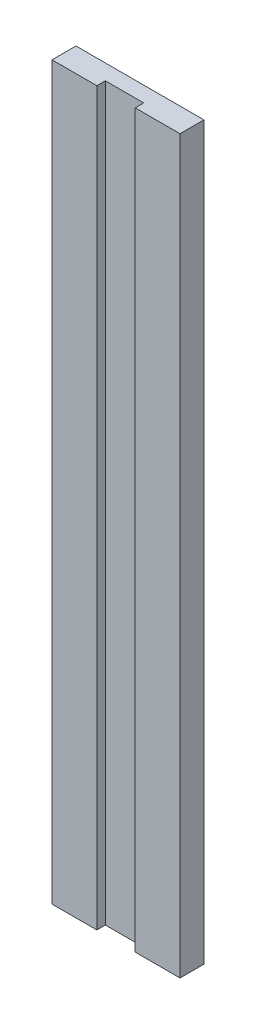
SolidWorks part; units mm, degrees
ref_plane "Front Plane" through (0, 0, 0) normal (0, 0, 1) x (1, 0, 0)
ref_plane "Top Plane" through (0, 0, 0) normal (0, 1, 0) x (1, 0, 0)
ref_plane "Right Plane" through (0, 0, 0) normal (1, 0, 0) x (0, 0, -1)
sketch "Sketch1" plane through (0, 0, 0) normal (0, 0, 1) x (1, 0, 0)
  line L1 (35, 200) -> (-35, 200)
  line L2 (35, 200) -> (35, -200)
  line L3 (35, -200) -> (-35, -200)
  line L4 (-35, 200) -> (-35, -200)
  line L5 (35, 200) -> (-35, -200) construction
  line L6 (35, -200) -> (-35, 200) construction
  point P0 (0, 0)
  dimension "D1" = 400
  dimension "D2" = 70
extrude "Boss-Extrude1" add sketch "Sketch1" along normal blind 8.45
sketch "Sketch3" plane through (0, 0, 8.45) normal (0, 0, 1) x (1, 0, 0)
  line L0 (-35, -200) -> (35, -200) construction
  line L1 (35, 200) -> (10.5, 200)
  line L2 (35, 200) -> (35, -200)
  line L3 (35, -200) -> (10.5, -200)
  line L4 (10.5, 200) -> (10.5, -200)
  line L5 (35, 200) -> (-35, 200) construction
  line L6 (-35, -200) -> (-10.5, -200)
  line L7 (-35, -200) -> (-35, 200)
  line L8 (-35, 200) -> (-10.5, 200)
  line L9 (-10.5, -200) -> (-10.5, 200)
  dimension "D1" = 21
extrude "Boss-Extrude2" add sketch "Sketch3" along normal blind 13.1 from surface at -8.45 starting at face at (0, 0, 0)
fillet "Fillet1" [suppressed] radius 5
sketch "Sketch4" plane through (0, 0, 13.1) normal (0, 0, 1) x (1, 0, 0)
  line L0 (-22.75, 200) -> (-22.75, 185) construction
  line L3 (-35, 200) -> (-10.5, 200) construction
  line L4 (-22.75, 185) -> (-22.75, 123.3333) construction
  line L5 (-22.75, 123.3333) -> (-22.75, 61.6667) construction
  line L6 (-22.75, 61.6667) -> (-22.75, 0) construction
  line L7 (-22.75, 0) -> (-22.75, -61.6667) construction
  line L8 (-22.75, -61.6667) -> (-22.75, -123.3333) construction
  line L9 (-22.75, -123.3333) -> (-22.75, -185) construction
  line L10 (-22.75, -185) -> (-22.75, -200) construction
  line L11 (-10.5, -200) -> (-35, -200) construction
  line L12 (0, 200) -> (0, -200) construction
  line L13 (10.5, 200) -> (-10.5, 200) construction
  line L14 (-10.5, -200) -> (10.5, -200) construction
  circle A0 centre (-22.75, 185) radius 2.75
  circle A1 centre (-22.75, 123.3333) radius 2.75
  circle A2 centre (-22.75, 61.6667) radius 2.75
  circle A3 centre (-22.75, 0) radius 2.75
  circle A4 centre (-22.75, -61.6667) radius 2.75
  circle A5 centre (-22.75, -123.3333) radius 2.75
  circle A6 centre (-22.75, -185) radius 2.75
  circle A7 centre (22.75, -185) radius 2.75
  circle A8 centre (22.75, -123.3333) radius 2.75
  circle A9 centre (22.75, -61.6667) radius 2.75
  circle A10 centre (22.75, 0) radius 2.75
  circle A11 centre (22.75, 61.6667) radius 2.75
  circle A12 centre (22.75, 123.3333) radius 2.75
  circle A13 centre (22.75, 185) radius 2.75
  dimension "D2" = 5.5
  dimension "D1" = 15
extrude "Cut-Extrude1" [suppressed] cut sketch "Sketch4" against normal through all
sketch "Sketch5" [suppressed] plane through (0, 0, 13.1) normal (0, 0, 1) x (1, 0, 0)
  circle A0 centre (-22.75, 185) radius 4.5
  circle A1 centre (22.75, 185) radius 4.5
  circle A2 centre (22.75, 123.3333) radius 4.5
  circle A3 centre (-22.75, 123.3333) radius 4.5
  circle A4 centre (-22.75, 61.6667) radius 4.5
  circle A5 centre (22.75, 61.6667) radius 4.5
  circle A6 centre (22.75, 0) radius 4.5
  circle A7 centre (-22.75, 0) radius 4.5
  circle A8 centre (-22.75, -61.6667) radius 4.5
  circle A9 centre (22.75, -61.6667) radius 4.5
  circle A10 centre (22.75, -123.3333) radius 4.5
  circle A11 centre (-22.75, -123.3333) radius 4.5
  circle A12 centre (-22.75, -185) radius 4.5
  circle A13 centre (22.75, -185) radius 4.5
  dimension "D1" = 9
extrude "Cut-Extrude2" [suppressed] cut sketch "Sketch5" against normal blind 5.5
sketch "Sketch6" [suppressed] plane through (0, 0, 13.1) normal (0, 0, 1) x (1, 0, 0)
  circle A0 centre (22.75, -123.3333) radius 3.3
  circle A1 centre (22.75, -185) radius 3.3
  dimension "D1" = 6.6
extrude "Cut-Extrude3" [suppressed] cut sketch "Sketch6" against normal through all
sketch "Sketch7" [suppressed] plane through (0, 0, 13.1) normal (0, 0, 1) x (1, 0, 0)
  circle A0 centre (22.75, -123.3333) radius 5.25
  circle A1 centre (22.75, -185) radius 5.25
  dimension "D1" = 10.5
extrude "Cut-Extrude4" [suppressed] cut sketch "Sketch7" against normal blind 6.4
sketch "Sketch8" [suppressed] plane through (0, 0, 13.1) normal (0, 0, 1) x (1, 0, 0)
  circle A0 centre (22.75, 185) radius 3.3
  circle A1 centre (22.75, 123.3333) radius 3.3
  dimension "D1" = 6.6
extrude "Cut-Extrude5" [suppressed] cut sketch "Sketch8" against normal through all
sketch "Sketch9" [suppressed] plane through (0, 0, 13.1) normal (0, 0, 1) x (1, 0, 0)
  circle A0 centre (22.75, 185) radius 5.25
  circle A1 centre (22.75, 123.3333) radius 5.25
  dimension "D1" = 10.5
extrude "Cut-Extrude6" [suppressed] cut sketch "Sketch9" against normal blind 6.4
equation "\"M5_Thread\"= 4.2mm"
equation "\"M5_Pass\"= 5.5"
equation "\"M6_Thread\"= 5mm"
equation "\"M6_Pass\"= 6.6"
equation "\"M5_Head\"= 9mm"
equation "\"M6_Head\"= 10.5"
equation "\"M5_HeadDepth\"= 5.5"
equation "\"M6_HeadDepth\"= 5.9 + .5"
equation "\"D2@Sketch4\"=\"M5_Pass\""
equation "\"D1@Sketch5\"=\"M5_Head\""
equation "\"D1@Cut-Extrude2\"=\"M5_HeadDepth\""
equation "\"D1@Sketch6\"=\"M6_Pass\""
equation "\"D1@Sketch7\"=\"M6_Head\""
equation "\"D1@Cut-Extrude4\"=\"M6_HeadDepth\""
equation "\"D1@Cut-Extrude6\"=\"M6_HeadDepth\""
